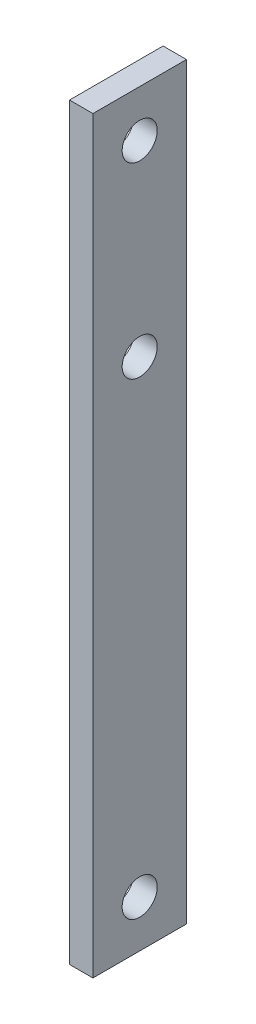
SolidWorks part; units mm, degrees
ref_plane "Front Plane" through (0, 0, 0) normal (0, 0, 1) x (1, 0, 0)
ref_plane "Top Plane" through (0, 0, 0) normal (0, 1, 0) x (1, 0, 0)
ref_plane "Right Plane" through (0, 0, 0) normal (1, 0, 0) x (0, 0, -1)
sketch "Sketch1" plane through (0, 0, 0) normal (1, 0, 0) x (0, 0, -1)
  line L1 (-25.4, -203.2) -> (25.4, -203.2)
  line L2 (-25.4, -203.2) -> (-25.4, 203.2)
  line L3 (-25.4, 203.2) -> (25.4, 203.2)
  line L4 (25.4, -203.2) -> (25.4, 203.2)
  line L5 (-25.4, -203.2) -> (25.4, 203.2) construction
  line L6 (-25.4, 203.2) -> (25.4, -203.2) construction
  point P0 (0, 0)
  dimension "D1" = 50.8
  dimension "D2" = 406.4
extrude "Boss-Extrude1" add sketch "Sketch1" along normal mid plane 12.7
sketch "Sketch2" plane through (6.35, 0, 0) normal (1, 0, 0) x (0, 0, -1)
  line L0 (0, 177.8) -> (0, -177.8) construction
  line L1 (25.4, 203.2) -> (-25.4, 203.2) construction
  circle A0 centre (0, 177.8) radius 9.525
  circle A1 centre (0, -177.8) radius 9.525
  circle A2 centre (0, 76.2) radius 9.525
  dimension "D1" = 19.05
  dimension "D2" = 25.4
  dimension "D3" = 101.6
extrude "Cut-Extrude1" cut sketch "Sketch2" against normal up to next
